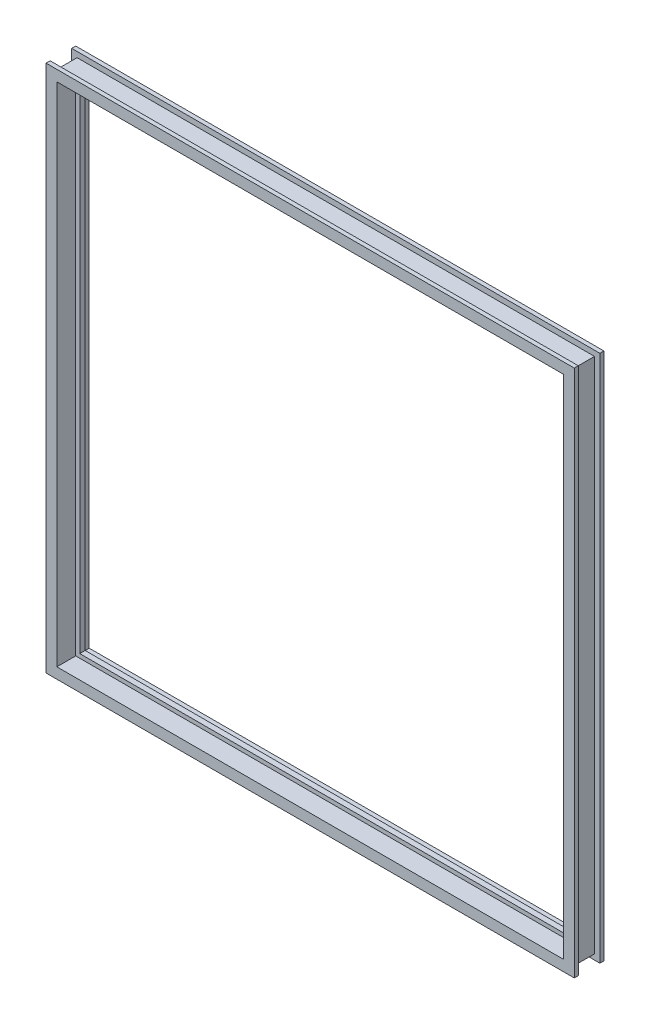
SolidWorks part; units mm, degrees
material "ABS"
ref_plane "Front Plane" through (0, 0, 0) normal (0, 0, 1) x (1, 0, 0)
ref_plane "Top Plane" through (0, 0, 0) normal (0, 1, 0) x (1, 0, 0)
ref_plane "Right Plane" through (0, 0, 0) normal (1, 0, 0) x (0, 0, -1)
sketch "Sketch1" plane through (0, 0, 0) normal (1, 0, 0) x (0, 0, -1)
  line L0 (-12.7, -6.35) -> (-17.4625, -6.35)
  line L1 (-17.4625, -6.35) -> (-17.4625, 6.35)
  line L2 (-17.4625, 6.35) -> (4.7625, 6.35)
  line L3 (4.7625, 6.35) -> (4.7625, 11.1125)
  line L4 (4.7625, 11.1125) -> (11.1125, 11.1125)
  line L5 (11.1125, 11.1125) -> (11.1125, 9.525)
  line L6 (11.1125, 9.525) -> (17.4625, 9.525)
  line L7 (17.4625, 9.525) -> (17.4625, -6.35)
  line L8 (17.4625, -6.35) -> (12.7, -6.35)
  line L9 (12.7, -6.35) -> (12.7, 0)
  line L10 (12.7, 0) -> (-12.7, 0)
  line L11 (-12.7, 0) -> (-12.7, -6.35)
  point P13 (0, 0)
  dimension "D1" = 25.4
  dimension "D2" = 4.7625
  dimension "D3" = 4.7625
  dimension "D4" = 6.35
  dimension "D5" = 6.35
  dimension "D6" = 6.35
  dimension "D7" = 6.35
  dimension "D8" = 4.7625
  dimension "D9" = 3.175
sketch "Sketch2" plane through (0, 0, 0) normal (0, 0, 1) x (1, 0, 0)
  line L1 (304.8, 609.6) -> (-304.8, 609.6)
  line L2 (304.8, 609.6) -> (304.8, 0)
  line L3 (304.8, 0) -> (-304.8, 0)
  line L4 (-304.8, 609.6) -> (-304.8, 0)
  line L5 (304.8, 609.6) -> (-304.8, 0) construction
  line L6 (304.8, 0) -> (-304.8, 609.6) construction
  point P0 (0, 304.8)
  point P5 (0, 0)
  dimension "D1" = 609.6
  dimension "D2" = 609.6
sweep "Sweep1" add profiles "Sketch1" path "Sketch2"
ref_plane "Plane5" through (0, 0, 15.875) normal (0, 0, 1) x (1, 0, 0)
sketch "Sketch4" plane through (0, 0, 15.875) normal (0, 0, 1) x (1, 0, 0)
  line L0 (-296.8625, 6.35) -> (-296.8625, 603.25) construction
  line L1 (298.45, 6.35) -> (-298.45, 6.35) construction
  line L2 (-298.45, 603.25) -> (298.45, 603.25) construction
  line L3 (-298.45, 6.35) -> (-298.45, 603.25) construction
  dimension "D1" = 1.5875
